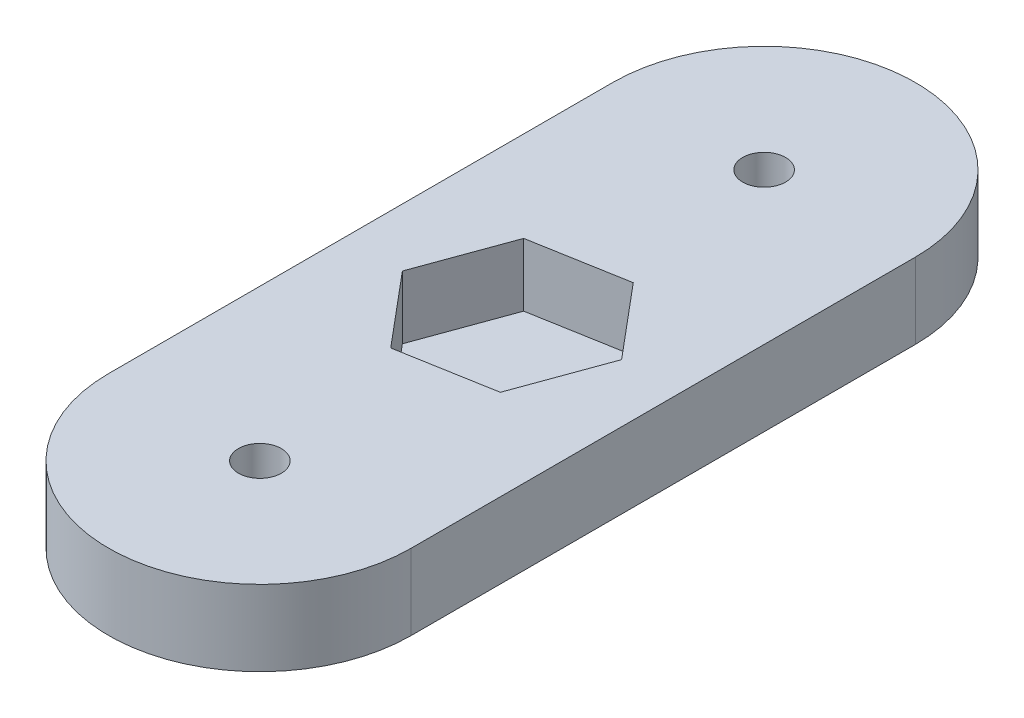
SolidWorks part; units mm, degrees
material "ABS PC"
ref_plane "Front Plane" through (0, 0, 0) normal (0, 0, 1) x (1, 0, 0)
ref_plane "Top Plane" through (0, 0, 0) normal (0, 1, 0) x (1, 0, 0)
ref_plane "Right Plane" through (0, 0, 0) normal (1, 0, 0) x (0, 0, -1)
sketch "Sketch1" plane through (0, 0, 0) normal (0, 1, 0) x (1, 0, 0)
  line L0 (0, 0) -> (0, 40) construction
  line L1 (-12, 0) -> (-12, 40)
  line L2 (12, 0) -> (12, 40)
  arc A0 (-12, 0) -> (12, 0) centre (0, 0) ccw
  arc A1 (12, 40) -> (-12, 40) centre (0, 40) ccw
  circle A2 centre (0, 40) radius 1.7
  circle A3 centre (0, 0) radius 1.7
  point P3 (0, 20)
  dimension "D2" = 40
  dimension "D3" = 3.4
  dimension "D1" = 24
extrude "Boss-Extrude1" add sketch "Sketch1" along normal blind 6
sketch "Sketch2" plane through (0, 6, 0) normal (0, 1, 0) x (1, 0, 0)
  line L0 (12, 0) -> (12, 40) construction
  line L1 (4.8245, 14.2504) -> (7.3915, 21.3033)
  line L2 (7.3915, 21.3033) -> (2.5671, 27.0529)
  line L3 (2.5671, 27.0529) -> (-4.8245, 25.7496)
  line L4 (-4.8245, 25.7496) -> (-7.3915, 18.6967)
  line L5 (-7.3915, 18.6967) -> (-2.5671, 12.9471)
  line L6 (-2.5671, 12.9471) -> (4.8245, 14.2504)
  line L7 (-12, 40) -> (-12, 0) construction
  circle A0 centre (0, 20) radius 6.5 construction
  dimension "D1" = 13
  dimension "D2" = 12
  dimension "D3" = 20
  dimension "D4" = 100
extrude "Cut-Extrude1" cut sketch "Sketch2" against normal blind 5
